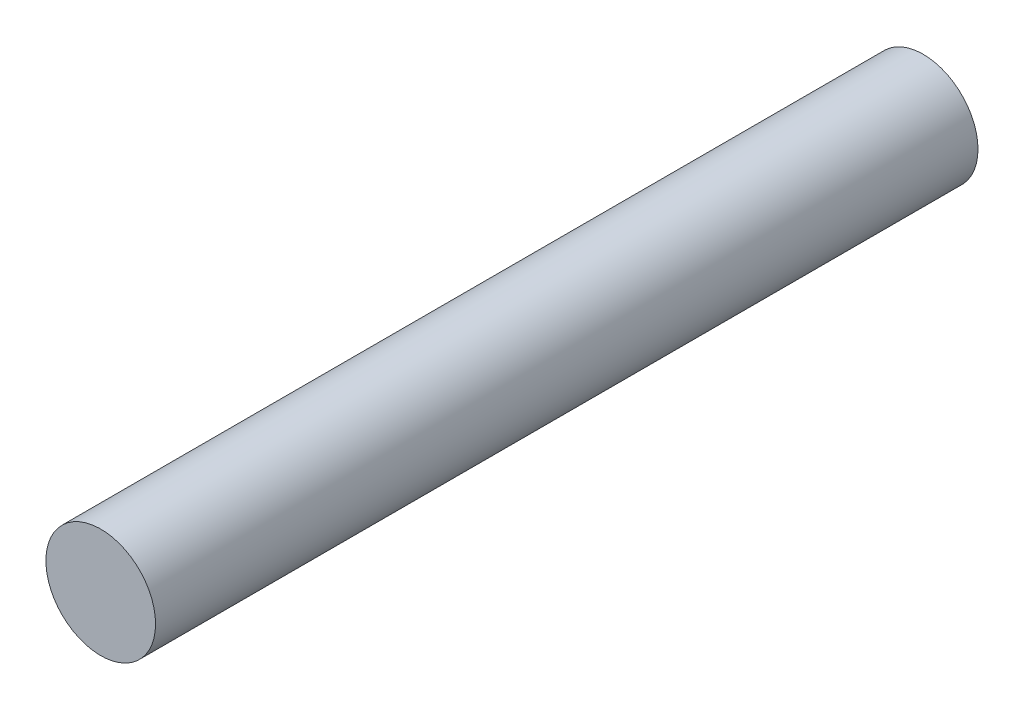
SolidWorks part; units mm, degrees
ref_plane "前视基准面" through (0, 0, 0) normal (0, 0, 1) x (1, 0, 0)
ref_plane "上视基准面" through (0, 0, 0) normal (0, 1, 0) x (1, 0, 0)
ref_plane "右视基准面" through (0, 0, 0) normal (1, 0, 0) x (0, 0, -1)
other "Configuration Table"
sketch "草图1" plane through (0, 0, 0) normal (0, 0, 1) x (1, 0, 0)
  circle A0 centre (0, 0) radius 4
extrude "凸台-拉伸1" add sketch "草图1" along normal blind 60
